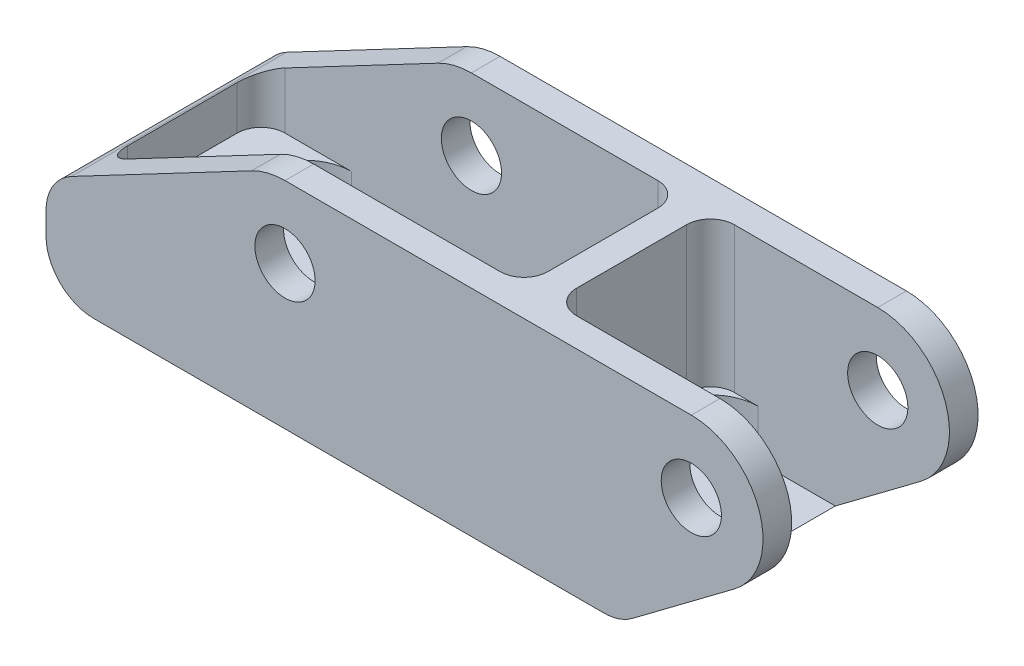
SolidWorks part; units mm, degrees
ref_plane "Front Plane" through (0, 0, 0) normal (0, 0, 1) x (1, 0, 0)
ref_plane "Top Plane" through (0, 0, 0) normal (0, 1, 0) x (1, 0, 0)
ref_plane "Right Plane" through (0, 0, 0) normal (1, 0, 0) x (0, 0, -1)
sketch "Sketch1" plane through (0, 0, 0) normal (0, 1, 0) x (1, 0, 0)
  line L0 (0, 6.35) -> (0, 22.225)
  line L1 (6.35, 28.575) -> (88.9, 28.575)
  line L3 (88.9, 0) -> (6.35, 0)
  line L4 (88.9, 28.575) -> (95.25, 28.575)
  line L5 (95.25, 28.575) -> (95.25, 0)
  line L6 (95.25, 0) -> (88.9, 0)
  line L7 (6.35, 28.575) -> (0, 28.575)
  line L8 (0, 28.575) -> (0, 22.225)
  line L9 (6.35, 0) -> (0, 0)
  line L10 (0, 0) -> (0, 6.35)
  circle A0 centre (12.7, 14.2875) radius 3
  circle A1 centre (50.8, 14.2875) radius 3
  point P0 (0, 0)
  point P1 (0, 28.575)
  point P2 (95.25, 28.575)
  point P3 (95.25, 0)
  point P6 (12.7, 14.2875)
  point P9 (50.8, 14.2875)
extrude "Boss-Extrude1" add sketch "Sketch1" against normal blind 28.575
sketch "Sketch2" plane through (0, 0, 0) normal (0, 1, 0) x (1, 0, 0)
  line L15 (3.81, 6.985) -> (3.81, 21.59)
  line L16 (6.985, 24.765) -> (56.515, 24.765)
  line L17 (59.69, 21.59) -> (59.69, 6.985)
  line L18 (56.515, 3.81) -> (6.985, 3.81)
  line L19 (63.5, 6.985) -> (63.5, 21.59)
  line L20 (66.675, 24.765) -> (95.25, 24.765)
  line L21 (95.25, 24.765) -> (95.25, 3.81)
  line L22 (95.25, 3.81) -> (66.675, 3.81)
  arc A10 (56.515, 3.81) -> (59.69, 6.985) centre (56.515, 6.985) ccw
  arc A11 (59.69, 21.59) -> (56.515, 24.765) centre (56.515, 21.59) ccw
  arc A12 (6.985, 24.765) -> (3.81, 21.59) centre (6.985, 21.59) ccw
  arc A13 (3.81, 6.985) -> (6.985, 3.81) centre (6.985, 6.985) ccw
  arc A14 (66.675, 24.765) -> (63.5, 21.59) centre (66.675, 21.59) ccw
  arc A15 (63.5, 6.985) -> (66.675, 3.81) centre (66.675, 6.985) ccw
  point P0 (5.08, 5.08)
  point P1 (5.08, 23.368)
  point P2 (58.42, 23.368)
  point P3 (58.42, 5.08)
  point P16 (63.5, 23.368)
  point P17 (63.5, 5.08)
  point P18 (95.25, 23.368)
  point P19 (95.25, 5.08)
  point P21 (3.81, 3.81)
  point P25 (3.81, 24.765)
  point P26 (59.69, 24.765)
  point P27 (59.69, 3.81)
  point P28 (63.5, 24.765)
  point P29 (63.5, 3.81)
  point P30 (95.25, 24.765)
  point P31 (95.25, 3.81)
  dimension "D1" = 3.175
  dimension "D2" = 3.175
extrude "Cut-Extrude1" cut sketch "Sketch2" against normal blind 19.304
sketch "Sketch9" plane through (0, -19.304, 0) normal (0, 1, 0) x (1, 0, 0)
  line L0 (7.6491, 18.136) -> (10.794, 22.2635)
  line L1 (15.8449, 24.765) -> (47.6551, 24.765)
  line L2 (7.6491, 10.439) -> (10.794, 6.3115)
  line L3 (15.8449, 3.81) -> (47.6551, 3.81)
  line L4 (55.8509, 18.136) -> (52.706, 22.2635)
  line L5 (55.8509, 10.439) -> (52.706, 6.3115)
  line L6 (63.5, 18.415) -> (63.5, 10.16)
  line L7 (69.85, 3.81) -> (95.25, 3.81)
  line L8 (95.25, 3.81) -> (95.25, 24.765)
  line L9 (95.25, 24.765) -> (69.85, 24.765)
  arc A0 (7.6491, 18.136) -> (7.6491, 10.439) centre (12.7, 14.2875) ccw
  arc A1 (55.8509, 10.439) -> (55.8509, 18.136) centre (50.8, 14.2875) ccw
  arc A2 (15.8449, 24.765) -> (10.794, 22.2635) centre (15.8449, 18.415) ccw
  arc A3 (10.794, 6.3115) -> (15.8449, 3.81) centre (15.8449, 10.16) ccw
  arc A4 (52.706, 6.3115) -> (47.6551, 3.81) centre (47.6551, 10.16) cw
  arc A5 (52.706, 22.2635) -> (47.6551, 24.765) centre (47.6551, 18.415) ccw
  arc A6 (63.5, 10.16) -> (69.85, 3.81) centre (69.85, 10.16) ccw
  arc A7 (63.5, 18.415) -> (69.85, 24.765) centre (69.85, 18.415) cw
  point P0 (12.7, 14.2875)
  point P1 (50.8, 14.2875)
  point P3 (63.5, 24.765)
  point P5 (95.25, 24.765)
  point P6 (12.7, 24.765)
  point P7 (12.7, 3.81)
  point P8 (50.8, 24.765)
  point P9 (50.8, 3.81)
  point P18 (95.25, 3.81)
  point P19 (63.5, 3.81)
  point P20 (63.5, 24.765)
  line M4 (56.515, 24.765) -> (6.985, 24.765)
  line M8 (6.985, 3.81) -> (56.515, 3.81)
  circle M9 centre (50.8, 14.2875) radius 3
  circle M10 centre (12.7, 14.2875) radius 3
  dimension "D1" = 6.35
extrude "Cut-Extrude7" cut sketch "Sketch9" against normal blind 6.35 contours L4 A5 A2 L0 A0 L2 A3 A4 L5 A1 M4 M8 M9 M10 | A7 L6 A6 L7 L8 L9
sketch "Sketch5" plane through (0, 0, -28.575) normal (0, 0, -1) x (-1, 0, 0)
  line L0 (-91.44, -17.145) -> (-77.8933, -27.305)
  line L1 (-74.0833, -28.575) -> (-95.25, -28.575)
  line L2 (-95.25, -28.575) -> (-95.25, 0)
  line L3 (-95.25, 0) -> (-85.725, 0)
  line L4 (-27.3084, -1.099) -> (-3.3889, -13.7076)
  line L5 (0, -19.3249) -> (0, -22.225)
  line L7 (-31.75, 0) -> (0, 0)
  line L8 (0, 0) -> (0, -19.3249)
  line L9 (0, -22.225) -> (0, -28.575)
  line L10 (0, -28.575) -> (-6.35, -28.575)
  circle A0 centre (-31.75, -9.525) radius 4
  circle A1 centre (-85.725, -9.525) radius 4
  arc A3 (-85.725, 0) -> (-91.44, -17.145) centre (-85.725, -9.525) ccw
  arc A4 (-77.8933, -27.305) -> (-74.0833, -28.575) centre (-74.0833, -22.225) ccw
  arc A5 (-27.3084, -1.099) -> (-31.75, 0) centre (-31.75, -9.525) ccw
  arc A6 (0, -22.225) -> (-6.35, -28.575) centre (-6.35, -22.225) cw
  arc A7 (0, -19.3249) -> (-3.3889, -13.7076) centre (-6.35, -19.3249) ccw
  point P0 (-31.75, -9.525)
  point P1 (-85.725, -9.525)
  point P6 (-76.2, -28.575)
  point P11 (0, -15.494)
  dimension "D1" = 6.35
  dimension "D2" = 6.35
extrude "Cut-Extrude3" cut sketch "Sketch5" against normal blind 28.575
